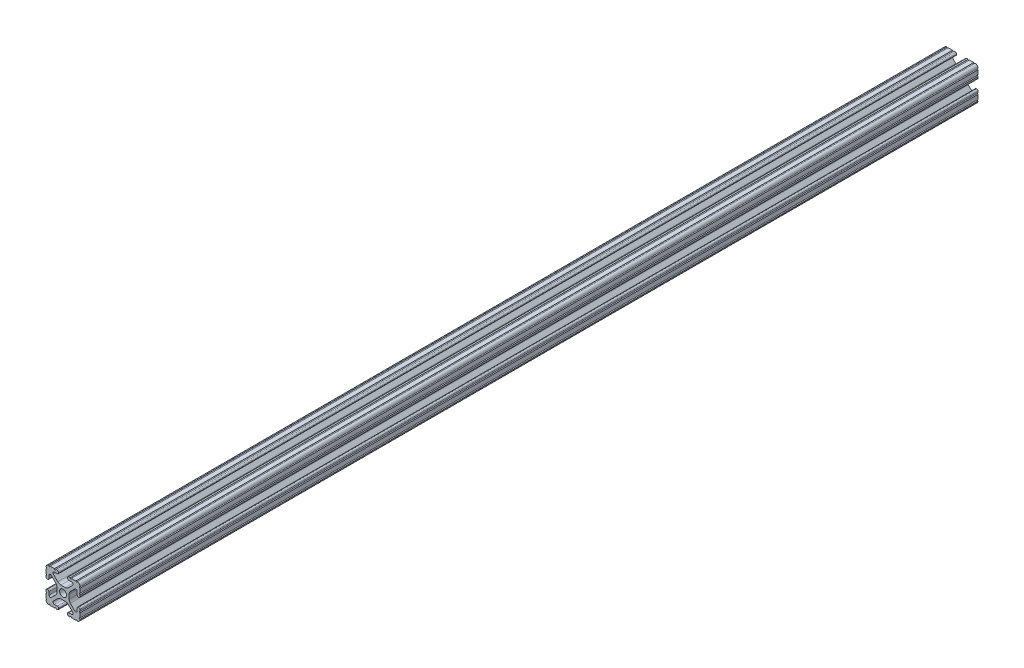
SolidWorks part; units mm, degrees
material "1060 Alloy"
ref_plane "Front Plane" through (0, 0, 0) normal (0, 0, 1) x (1, 0, 0)
ref_plane "Top Plane" through (0, 0, 0) normal (0, 1, 0) x (1, 0, 0)
ref_plane "Right Plane" through (0, 0, 0) normal (1, 0, 0) x (0, 0, -1)
sketch "Sketch1" plane through (0, 0, 0) normal (0, 0, 1) x (1, 0, 0)
  line L88 (-7.1797, -8.6452) -> (-3.9523, -5.4237)
  line L89 (-1.7093, -4.4958) -> (1.7093, -4.4958)
  line L90 (3.9523, -5.4237) -> (7.1797, -8.6452)
  line L91 (6.4164, -10.4902) -> (4.2875, -10.4902)
  line L92 (3.2385, -11.5392) -> (3.2385, -11.651)
  line L93 (4.2875, -12.7) -> (5.3171, -12.7)
  line L94 (6.3331, -12.7) -> (9.5504, -12.7)
  line L95 (12.7, -9.5504) -> (12.7, -6.3331)
  line L96 (12.7, -5.3171) -> (12.7, -4.2875)
  line L97 (11.651, -3.2385) -> (11.5392, -3.2385)
  line L98 (10.4902, -4.2875) -> (10.4902, -6.4021)
  line L99 (8.7371, -7.1294) -> (5.441, -3.8408)
  line L100 (4.5085, -1.5932) -> (4.5085, 1.5932)
  line L101 (5.441, 3.8408) -> (8.7371, 7.1294)
  line L102 (10.4902, 6.4021) -> (10.4902, 4.2875)
  line L103 (11.5392, 3.2385) -> (11.651, 3.2385)
  line L104 (12.7, 4.2875) -> (12.7, 5.3171)
  line L105 (12.7, 6.3331) -> (12.7, 9.5504)
  line L106 (9.5504, 12.7) -> (6.3331, 12.7)
  line L107 (5.3171, 12.7) -> (4.2875, 12.7)
  line L108 (3.2385, 11.651) -> (3.2385, 11.5392)
  line L109 (4.2875, 10.4902) -> (6.4768, 10.4902)
  line L110 (7.207, 8.7244) -> (3.8983, 5.4232)
  line L111 (1.6558, 4.4958) -> (-1.6558, 4.4958)
  line L112 (-3.8983, 5.4232) -> (-7.207, 8.7244)
  line L113 (-6.4768, 10.4902) -> (-4.2875, 10.4902)
  line L114 (-3.2385, 11.5392) -> (-3.2385, 11.651)
  line L115 (-4.2875, 12.7) -> (-5.3171, 12.7)
  line L116 (-6.3331, 12.7) -> (-9.5504, 12.7)
  line L117 (-12.7, 9.5504) -> (-12.7, 6.3331)
  line L118 (-12.7, 5.3171) -> (-12.7, 4.2875)
  line L119 (-11.651, 3.2385) -> (-11.5392, 3.2385)
  line L120 (-10.4902, 4.2875) -> (-10.4902, 6.4021)
  line L121 (-8.7371, 7.1294) -> (-5.441, 3.8408)
  line L122 (-4.5085, 1.5932) -> (-4.5085, -1.5932)
  line L123 (-5.441, -3.8408) -> (-8.7371, -7.1294)
  line L124 (-10.4902, -6.4021) -> (-10.4902, -4.2875)
  line L125 (-11.5392, -3.2385) -> (-11.651, -3.2385)
  line L126 (-12.7, -4.2875) -> (-12.7, -5.3171)
  line L127 (-12.7, -6.3331) -> (-12.7, -9.5504)
  line L128 (-9.5504, -12.7) -> (-6.3331, -12.7)
  line L129 (-5.3171, -12.7) -> (-4.2875, -12.7)
  line L130 (-3.2385, -11.651) -> (-3.2385, -11.5392)
  line L131 (-4.2875, -10.4902) -> (-6.4164, -10.4902)
  circle A1 centre (0, 0) radius 2.6035
  arc A104 (-7.1797, -8.6452) -> (-6.4164, -10.4902) centre (-6.4164, -9.4098) ccw
  arc A105 (-1.7093, -4.4958) -> (-3.9523, -5.4237) centre (-1.7093, -7.6708) ccw
  arc A106 (3.9523, -5.4237) -> (1.7093, -4.4958) centre (1.7093, -7.6708) ccw
  arc A107 (6.4164, -10.4902) -> (7.1797, -8.6452) centre (6.4164, -9.4098) ccw
  arc A108 (4.2875, -10.4902) -> (3.2385, -11.5392) centre (4.2875, -11.5392) ccw
  arc A109 (3.2385, -11.651) -> (4.2875, -12.7) centre (4.2875, -11.651) ccw
  arc A110 (6.3331, -12.7) -> (5.3171, -12.7) centre (5.8251, -12.7) ccw
  arc A111 (10.5664, -12.6998) -> (9.5504, -12.7) centre (10.0584, -12.7) ccw
  arc A112 (10.5664, -12.6998) -> (12.6998, -10.5664) centre (10.5918, -10.5918) ccw
  arc A113 (12.7, -9.5504) -> (12.6998, -10.5664) centre (12.7, -10.0584) ccw
  arc A114 (12.7, -5.3171) -> (12.7, -6.3331) centre (12.7, -5.8251) ccw
  arc A115 (12.7, -4.2875) -> (11.651, -3.2385) centre (11.651, -4.2875) ccw
  arc A116 (11.5392, -3.2385) -> (10.4902, -4.2875) centre (11.5392, -4.2875) ccw
  arc A117 (8.7371, -7.1294) -> (10.4902, -6.4021) centre (9.4628, -6.4021) ccw
  arc A118 (4.5085, -1.5932) -> (5.441, -3.8408) centre (7.6835, -1.5932) ccw
  arc A119 (5.441, 3.8408) -> (4.5085, 1.5932) centre (7.6835, 1.5932) ccw
  arc A120 (10.4902, 6.4021) -> (8.7371, 7.1294) centre (9.4628, 6.4021) ccw
  arc A121 (10.4902, 4.2875) -> (11.5392, 3.2385) centre (11.5392, 4.2875) ccw
  arc A122 (11.651, 3.2385) -> (12.7, 4.2875) centre (11.651, 4.2875) ccw
  arc A123 (12.7, 6.3331) -> (12.7, 5.3171) centre (12.7, 5.8251) ccw
  arc A124 (12.6998, 10.5664) -> (12.7, 9.5504) centre (12.7, 10.0584) ccw
  arc A125 (12.6998, 10.5664) -> (10.5664, 12.6998) centre (10.5918, 10.5918) ccw
  arc A126 (9.5504, 12.7) -> (10.5664, 12.6998) centre (10.0584, 12.7) ccw
  arc A127 (5.3171, 12.7) -> (6.3331, 12.7) centre (5.8251, 12.7) ccw
  arc A128 (4.2875, 12.7) -> (3.2385, 11.651) centre (4.2875, 11.651) ccw
  arc A129 (3.2385, 11.5392) -> (4.2875, 10.4902) centre (4.2875, 11.5392) ccw
  arc A130 (7.207, 8.7244) -> (6.4768, 10.4902) centre (6.4768, 9.4563) ccw
  arc A131 (1.6558, 4.4958) -> (3.8983, 5.4232) centre (1.6558, 7.6708) ccw
  arc A132 (-3.8983, 5.4232) -> (-1.6558, 4.4958) centre (-1.6558, 7.6708) ccw
  arc A133 (-6.4768, 10.4902) -> (-7.207, 8.7244) centre (-6.4768, 9.4563) ccw
  arc A134 (-4.2875, 10.4902) -> (-3.2385, 11.5392) centre (-4.2875, 11.5392) ccw
  arc A135 (-3.2385, 11.651) -> (-4.2875, 12.7) centre (-4.2875, 11.651) ccw
  arc A136 (-6.3331, 12.7) -> (-5.3171, 12.7) centre (-5.8251, 12.7) ccw
  arc A137 (-10.5664, 12.6998) -> (-9.5504, 12.7) centre (-10.0584, 12.7) ccw
  arc A138 (-10.5664, 12.6998) -> (-12.6998, 10.5664) centre (-10.5918, 10.5918) ccw
  arc A139 (-12.7, 9.5504) -> (-12.6998, 10.5664) centre (-12.7, 10.0584) ccw
  arc A140 (-12.7, 5.3171) -> (-12.7, 6.3331) centre (-12.7, 5.8251) ccw
  arc A141 (-12.7, 4.2875) -> (-11.651, 3.2385) centre (-11.651, 4.2875) ccw
  arc A142 (-11.5392, 3.2385) -> (-10.4902, 4.2875) centre (-11.5392, 4.2875) ccw
  arc A143 (-8.7371, 7.1294) -> (-10.4902, 6.4021) centre (-9.4628, 6.4021) ccw
  arc A144 (-4.5085, 1.5932) -> (-5.441, 3.8408) centre (-7.6835, 1.5932) ccw
  arc A145 (-5.441, -3.8408) -> (-4.5085, -1.5932) centre (-7.6835, -1.5932) ccw
  arc A146 (-10.4902, -6.4021) -> (-8.7371, -7.1294) centre (-9.4628, -6.4021) ccw
  arc A147 (-10.4902, -4.2875) -> (-11.5392, -3.2385) centre (-11.5392, -4.2875) ccw
  arc A148 (-11.651, -3.2385) -> (-12.7, -4.2875) centre (-11.651, -4.2875) ccw
  arc A149 (-12.7, -6.3331) -> (-12.7, -5.3171) centre (-12.7, -5.8251) ccw
  arc A150 (-12.6998, -10.5664) -> (-12.7, -9.5504) centre (-12.7, -10.0584) ccw
  arc A151 (-12.6998, -10.5664) -> (-10.5664, -12.6998) centre (-10.5918, -10.5918) ccw
  arc A152 (-9.5504, -12.7) -> (-10.5664, -12.6998) centre (-10.0584, -12.7) ccw
  arc A153 (-5.3171, -12.7) -> (-6.3331, -12.7) centre (-5.8251, -12.7) ccw
  arc A154 (-4.2875, -12.7) -> (-3.2385, -11.651) centre (-4.2875, -11.651) ccw
  arc A155 (-3.2385, -11.5392) -> (-4.2875, -10.4902) centre (-4.2875, -11.5392) ccw
extrude "Boss-Extrude1" add sketch "Sketch1" along normal blind 670
